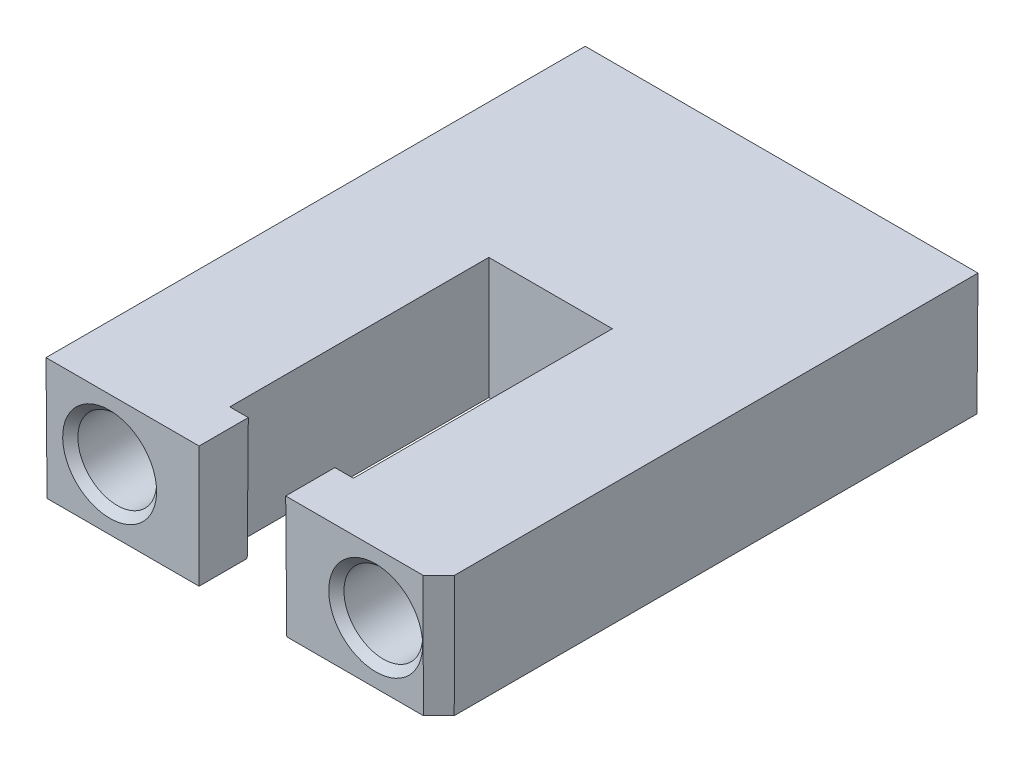
SolidWorks part; units mm, degrees
ref_plane "Front" through (0, 0, 0) normal (0, 0, 1) x (1, 0, 0)
ref_plane "Top" through (0, 0, 0) normal (0, 1, 0) x (1, 0, 0)
ref_plane "Right" through (0, 0, 0) normal (1, 0, 0) x (0, 0, -1)
sketch "Sketch1" plane through (0, 0, 0) normal (0, 0, 1) x (1, 0, 0)
  line L0 (10.5698, 0) -> (0, 0) construction
  line L1 (-12.6746, 3.937) -> (12.6746, 3.937)
  line L2 (-12.6746, 3.937) -> (-12.6746, -3.937)
  line L3 (-12.6746, -3.937) -> (12.6746, -3.937)
  line L4 (12.6746, 3.937) -> (12.6746, -3.937)
  line L5 (0, 0) -> (0, 18.3581) construction
  dimension "D1" = 7.874
  dimension "D2" = 25.3492
extrude "Boss-Extrude1" add sketch "Sketch1" against normal blind 34.798
sketch "Sketch2" plane through (0, 3.937, 0) normal (0, 1, 0) x (1, 0, 0)
  line L0 (0, 0) -> (0, 14.9083) construction
  line L1 (-2.794, 0) -> (-2.794, 3.175)
  line L2 (12.6746, 0) -> (-12.6746, 0) construction
  line L3 (-2.794, 3.175) -> (-3.9878, 3.175)
  line L4 (-3.9878, 3.175) -> (-3.9878, 19.8882)
  line L5 (-3.9878, 19.8882) -> (3.9878, 19.8882)
  line L6 (3.9878, 19.8882) -> (3.9878, 3.175)
  line L7 (3.9878, 3.175) -> (2.794, 3.175)
  line L8 (2.794, 3.175) -> (2.794, 0)
  line L9 (-2.794, 0) -> (2.794, 0)
  dimension "D1" = 5.588
  dimension "D2" = 3.175
  dimension "D3" = 19.8882
  dimension "D4" = 7.9756
extrude "Cut-Extrude1" cut sketch "Sketch2" against normal through all
sketch "Sketch3" plane through (0, 0, 0) normal (0, 0, 1) x (1, 0, 0)
  line L0 (2.794, -3.937) -> (12.6746, -3.937) construction
  point P0 (-8.5852, 0)
  point P1 (8.5852, 0)
  dimension "D1" = 8.5852
  dimension "D2" = 8.5852
  dimension "D3" = 3.937
hole_wizard "#97 (0.0059) Diameter Hole1" positions "Sketch5" profile "Sketch4" hole size "#97" standard "ANSI Inch"
sketch "Sketch5" plane through (0, 0, 0) normal (0, 0, 1) x (1, 0, 0)
  point P0 (-8.5852, 0)
  point P3 (8.5852, 0)
sketch "Sketch4" plane through (-8.5852, 0, 0) normal (1, 0, 0) x (0, -1, 0)
  line L0 (0, 0) -> (0, 14.2262)
  line L1 (0, 14.2262) -> (2.54, 12.7)
  line L2 (2.54, 12.7) -> (2.54, 0)
  line L5 (2.54, 0) -> (0, 0)
  line L10 (0, 14.2262) -> (-2.54, 12.7) construction
  line L11 (0, -6.35) -> (0, 107.95) construction
  dimension "Hole Dia." = 5.08
  dimension "Hole Depth" = 12.7
  dimension "Drill Angle" = 118
chamfer "Chamfer1" distance 0.508 angle 45 2 edges at (11.1252, 0, 0) (-6.0452, 0, 0)
chamfer "Chamfer2" distance 1.016 angle 45 1 edges at (12.6746, 0, 0)
draft "Draft1" type of draft neutral plane draft angle 0.25 faces to draft 13 face at (12.1666, 0, -0.508) face at (11.6332, 0, 0) face at (-5.5372, 0, 0) face at (0, 0, -34.798) face at (-12.6746, 0, -17.399) face at (12.6746, 0, -17.907) face at (-3.3909, 0, -3.175) face at (3.3909, 0, -3.175) face at (2.794, 0, -1.5875) face at (3.9878, 0, -11.5316) face at (-2.794, 0, -1.5875) face at (0, 0, -19.8882) face at (-3.9878, 0, -11.5316) neutral plane through (-12.6746, 3.937, -34.798) neutral plane normal (0, 1, 0) reverse direction yes parameters "D1"=0.25
